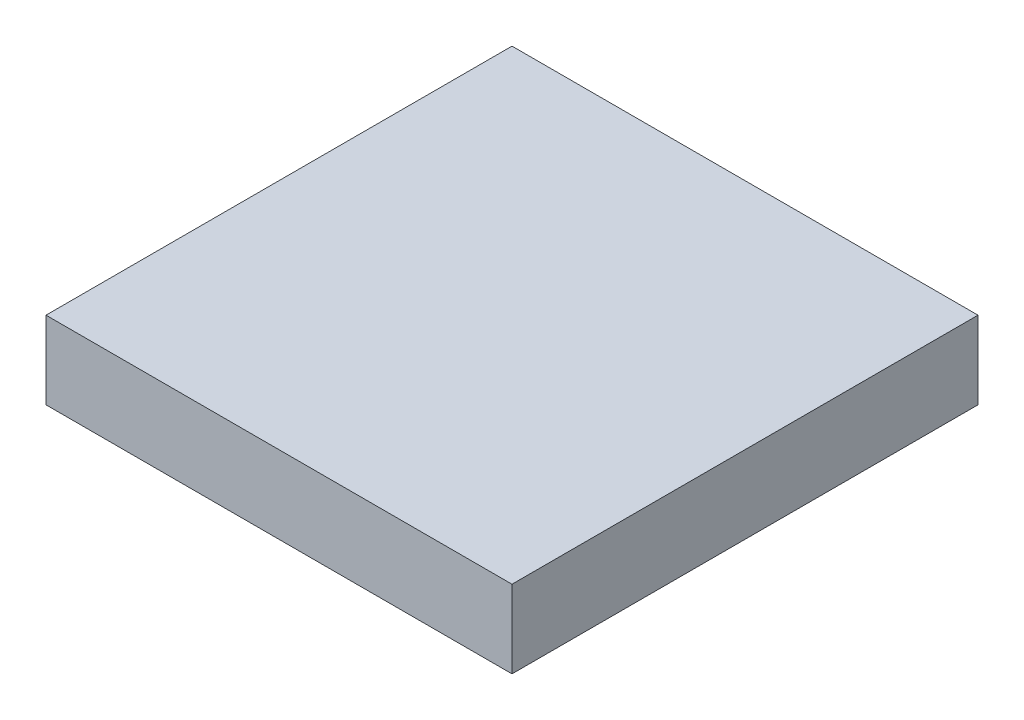
SolidWorks part; units mm, degrees
ref_plane "Front Plane" through (0, 0, 0) normal (0, 0, 1) x (1, 0, 0)
ref_plane "Top Plane" through (0, 0, 0) normal (0, 1, 0) x (1, 0, 0)
ref_plane "Right Plane" through (0, 0, 0) normal (1, 0, 0) x (0, 0, -1)
sketch "Sketch1" plane through (0, 0, 0) normal (0, 1, 0) x (1, 0, 0)
  line L1 (0, 12) -> (12, 12)
  line L2 (0, 12) -> (0, 0)
  line L3 (0, 0) -> (12, 0)
  line L4 (12, 12) -> (12, 0)
  dimension "D1" = 12
  dimension "D2" = 12
extrude "Boss-Extrude1" add sketch "Sketch1" along normal blind 2
sketch3d "3DSketch2" plane through (0, 0, 0) normal (0, 0, 1) x (1, 0, 0)
  dimension "D1" = 0.5
sketch "Sketch2" plane through (0, 1.5, 0) normal (0, 1, 0) x (1, 0, 0)
  line L0 (0, 12) -> (0, 0) construction
  line L1 (2, 10) -> (10, 10)
  line L2 (2, 10) -> (2, 2)
  line L3 (2, 2) -> (10, 2)
  line L4 (10, 10) -> (10, 2)
  line L5 (0, 0) -> (12, 0) construction
  dimension "D1" = 2
  dimension "D2" = 2
  dimension "D3" = 8
  dimension "D4" = 8
